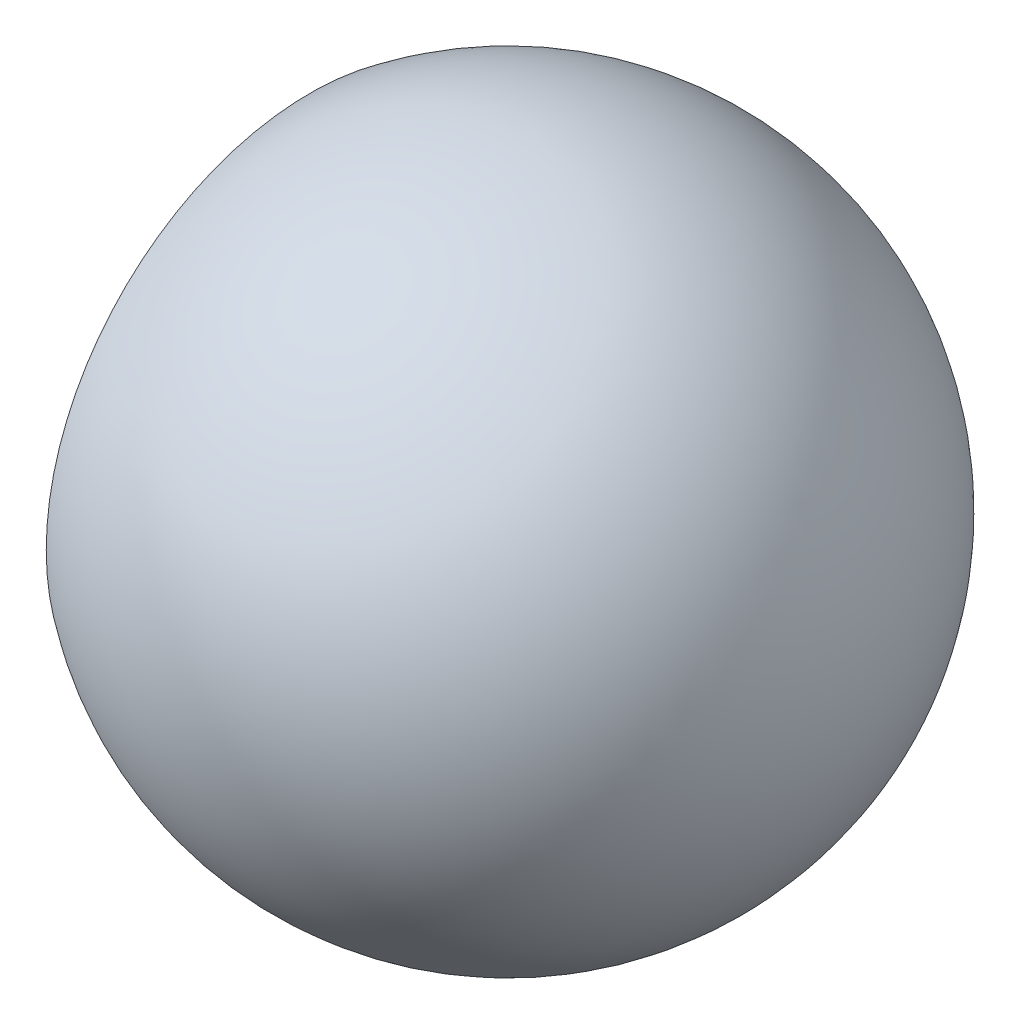
SolidWorks part; units mm, degrees
material "Резина"
ref_plane "Спереди" through (0, 0, 0) normal (0, 0, 1) x (1, 0, 0)
ref_plane "Сверху" through (0, 0, 0) normal (0, 1, 0) x (1, 0, 0)
ref_plane "Справа" through (0, 0, 0) normal (1, 0, 0) x (0, 0, -1)
sketch "Эскиз5" plane through (0, 0, 0) normal (0, 0, 1) x (1, 0, 0)
  line L0 (0, 0) -> (10, 0)
  line L1 (0, 0) -> (0, -4)
  line L2 (0, -4) -> (-6, -4)
  line L3 (-6, -4) -> (-6, -8)
  arc A0 (-6, -8) -> (10, 0) centre (0, 0) ccw
  dimension "D1" = 20
  dimension "D2" = 4
  dimension "D3" = 6
revolve "Повернуть2" add sketch "Эскиз5" angle 360 about L0
